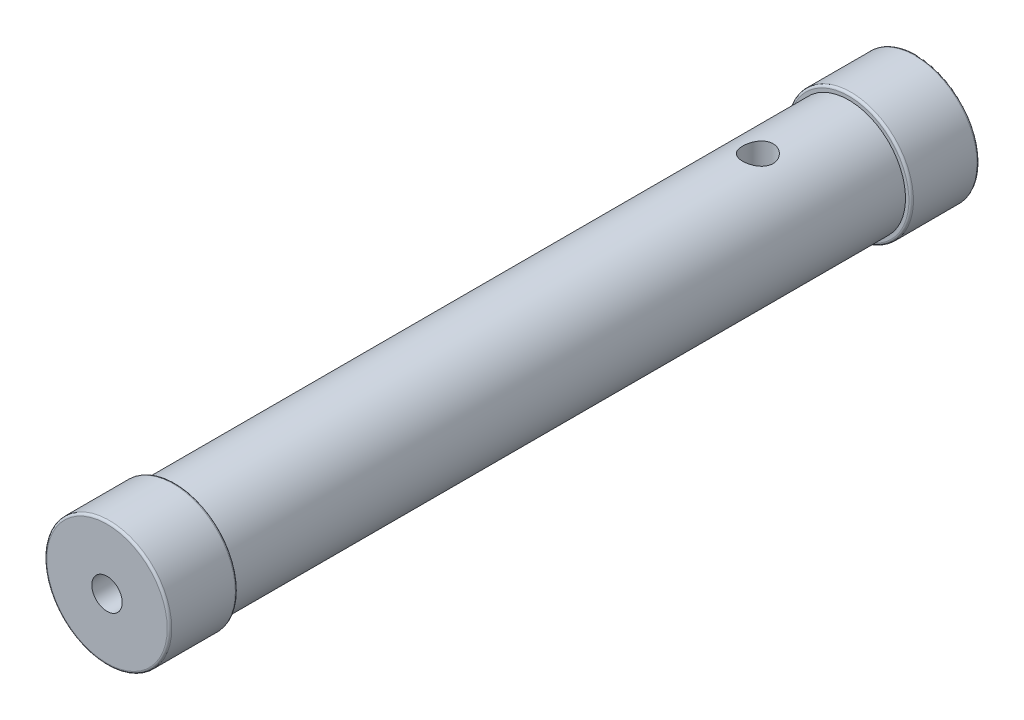
SolidWorks part; units mm, degrees
ref_plane "Front Plane" through (0, 0, 0) normal (1, 0, 0) x (0, 1, 0)
ref_plane "Top Plane" through (0, 0, 0) normal (0, 0, 1) x (0, 1, 0)
ref_plane "Right Plane" through (0, 0, 0) normal (0, 1, 0) x (-1, 0, 0)
sketch "Sketch1" plane through (0, 0, 0) normal (0, 0, 1) x (0, 1, 0)
  circle A0 centre (0, 0) radius 25
  dimension "D1" = 50
extrude "Boss-Extrude1" add sketch "Sketch1" along normal blind 356.5
sketch "Sketch2" plane through (0, 0, 356.5) normal (0, 0, 1) x (1, 0, 0)
  circle A0 centre (0, 0) radius 27.5
  dimension "D1" = 55
extrude "Boss-Extrude2" add sketch "Sketch2" against normal blind 30
sketch "Sketch3" plane through (0, 0, 0) normal (0, 0, -1) x (-1, 0, 0)
  circle A0 centre (0, 0) radius 27.5
  dimension "D1" = 55
extrude "Boss-Extrude3" add sketch "Sketch3" against normal blind 30
sketch "Sketch4" plane through (0, 0, 0) normal (0, 0, -1) x (1, 0, 0)
  circle A0 centre (0, 0) radius 6.7
  dimension "D1" = 13.4
extrude "Cut-Extrude1" cut sketch "Sketch4" against normal blind 20
sketch "Sketch5" plane through (0, 0, 356.5) normal (0, 0, 1) x (1, 0, 0)
  circle A0 centre (0, 0) radius 6.7
  dimension "D1" = 13.4
extrude "Cut-Extrude2" cut sketch "Sketch5" against normal blind 20
ref_plane "Plane1" through (0, 25, 0) normal (0, 1, 0) x (-1, 0, 0)
sketch "Sketch6" plane through (0, 25, 0) normal (0, 1, 0) x (-1, 0, 0)
  line L0 (-27.5, 0) -> (27.5, 0) construction
  circle A0 centre (0, 70) radius 6.7
  point P5 (0, 0)
  dimension "D1" = 13.4
  dimension "D2" = 70
extrude "Cut-Extrude3" cut sketch "Sketch6" against normal blind 20
fillet "Fillet1" radius 1 4 edges at (-27.5, 0, 30) (-27.5, 0, 0) (27.5, 0, 326.5) (27.5, 0, 356.5)
